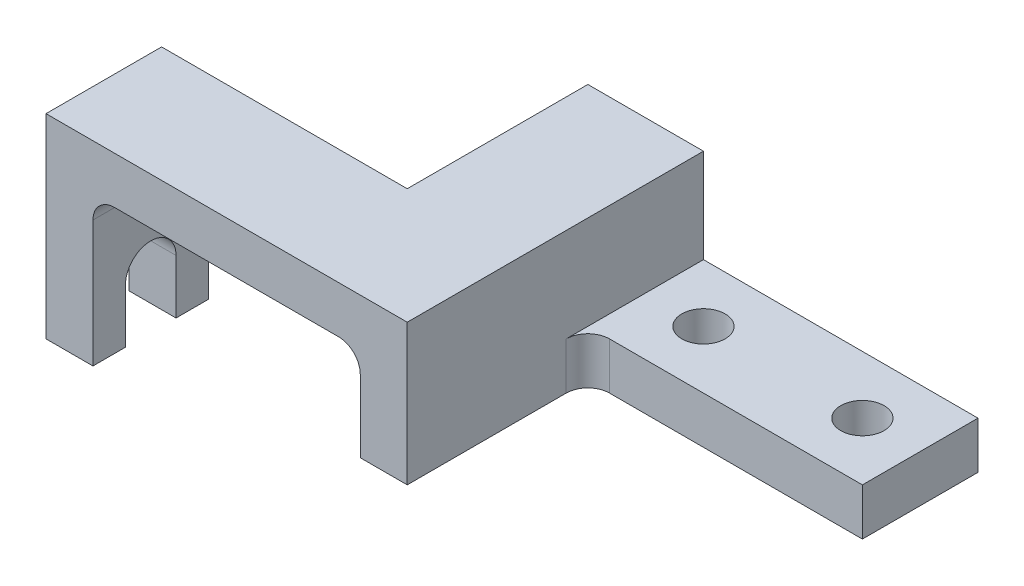
SolidWorks part; units mm, degrees
ref_plane "Front Plane" through (0, 0, 0) normal (0, 0, 1) x (1, 0, 0)
ref_plane "Top Plane" through (0, 0, 0) normal (0, 1, 0) x (1, 0, 0)
ref_plane "Right Plane" through (0, 0, 0) normal (1, 0, 0) x (0, 0, -1)
sketch "Sketch1" plane through (0, 0, 0) normal (0, 1, 0) x (1, 0, 0)
  line L1 (-38, -16) -> (38, -16)
  line L2 (-38, -16) -> (-38, 16)
  line L3 (-38, 16) -> (38, 16)
  line L4 (38, -16) -> (38, 16)
  line L5 (-38, -16) -> (38, 16) construction
  line L6 (-38, 16) -> (38, -16) construction
  point P0 (0, 0)
  dimension "D1" = 76
  dimension "D2" = 32
extrude "Boss-Extrude1" add sketch "Sketch1" along normal blind 13
sketch "Sketch2" plane through (0, 13, 0) normal (0, 1, 0) x (1, 0, 0)
  line L0 (-38, 0) -> (38, 0) construction
  line L1 (-38, 16) -> (-38, -16) construction
  line L2 (38, -16) -> (38, 16) construction
  circle A0 centre (-22, 0) radius 6
  circle A1 centre (22, 0) radius 6
  point P12 (42.9603, 2.694)
  dimension "D1" = 12
  dimension "D2" = 44
  dimension "D3" = 16
extrude "Cut-Extrude1" cut sketch "Sketch2" against normal through all both and the other way through all
sketch "Sketch3" plane through (-38, 0, 0) normal (-1, 0, 0) x (0, 0, 1)
  line L1 (-16, 0) -> (66, 0)
  line L2 (-16, 0) -> (-16, 39)
  line L3 (-16, 39) -> (66, 39)
  line L4 (66, 0) -> (66, 39)
  dimension "D1" = 82
  dimension "D2" = 39
extrude "Boss-Extrude2" add sketch "Sketch3" along normal blind 13
sketch "Sketch4" plane through (-51, 0, 0) normal (-1, 0, 0) x (0, 0, 1)
  line L0 (66, 0) -> (66, 39) construction
  line L1 (-16, 39) -> (66, 39)
  line L2 (-16, 39) -> (-16, 26)
  line L3 (-16, 26) -> (66, 26)
  line L4 (66, 39) -> (66, 26)
  dimension "D1" = 13
extrude "Boss-Extrude3" add sketch "Sketch4" along normal blind 87
sketch "Sketch5" plane through (0, 39, 0) normal (0, 1, 0) x (1, 0, 0)
  line L0 (-138, -34) -> (-70, -34)
  line L1 (-138, -66) -> (-138, 16) construction
  line L2 (-70, -34) -> (-70, 16)
  line L4 (-38, -66) -> (-38, 16) construction
  line L5 (-138, -66) -> (-38, -66) construction
  line L6 (-138, 16) -> (-38, 16) construction
  line L11 (-38, -66) -> (-38, 16)
  line L12 (-38, 16) -> (-138, 16)
  line L13 (-138, 16) -> (-138, -66)
  line L14 (-138, -66) -> (-38, -66)
  line L15 (-38, -66) -> (-38, 16)
  line L16 (-38, 16) -> (-138, 16)
  line L17 (-138, 16) -> (-138, -66)
  line L18 (-138, -66) -> (-38, -66)
  point P9 (-70, 16)
  line M2 (-38, 16) -> (-138, 16)
  line M3 (-138, 16) -> (-138, -66)
  dimension "D1" = 32
  dimension "D2" = 32
  dimension "D3" = 0
extrude "Cut-Extrude2" cut sketch "Sketch5" against normal through all both and the other way through all contours L0 L2 M2 M3
sketch "Sketch6" plane through (0, 26, 0) normal (0, -1, 0) x (1, 0, 0)
  line L0 (-138, 34) -> (-70, 34) construction
  line L1 (-138, 66) -> (-125, 66)
  line L2 (-138, 66) -> (-138, 34)
  line L3 (-138, 34) -> (-125, 34)
  line L4 (-125, 66) -> (-125, 34)
  dimension "D1" = 13
extrude "Boss-Extrude4" add sketch "Sketch6" along normal blind 41
fillet "Fillet1" radius 6 3 edges at (-38, 6.5, 16) (-125, 26, 50) (-51, 26, 25)
sketch "Sketch7" plane through (-138, 0, 0) normal (-1, 0, 0) x (0, 0, 1)
  line L0 (50, -15) -> (50, 39) construction
  line L1 (66, -15) -> (34, -15) construction
  line L2 (66, 39) -> (34, 39) construction
  line L3 (43, 0) -> (43, -15)
  line L4 (57, 0) -> (57, -15)
  line L5 (57, -15) -> (43, -15)
  arc A0 (57, 0) -> (43, 0) centre (50, 0) ccw
  point P11 (57, -15)
  dimension "D1" = 14
  dimension "D2" = 15
extrude "Cut-Extrude3" cut sketch "Sketch7" against normal up to next and the other way through all
